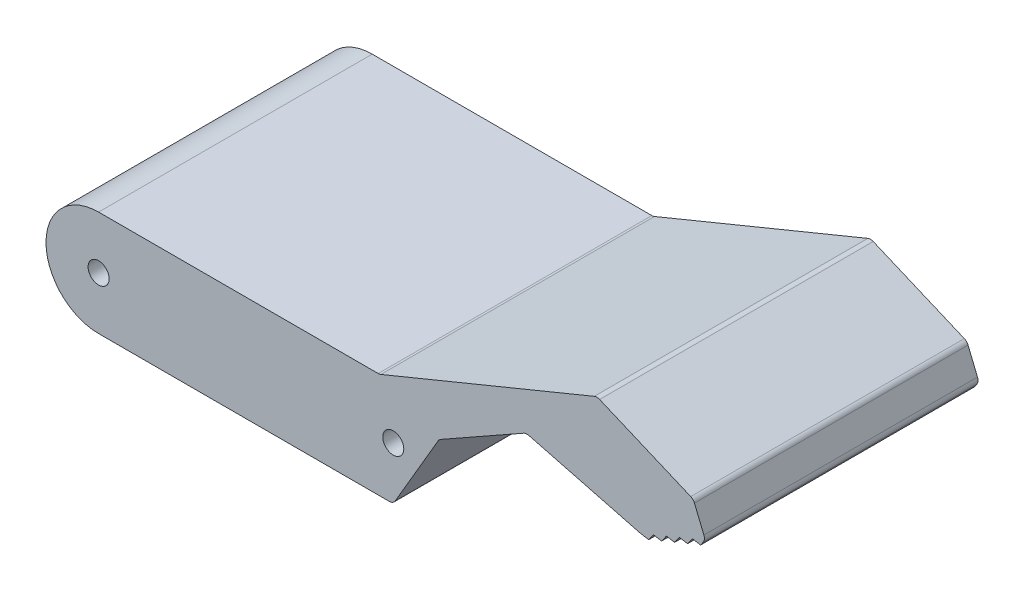
SolidWorks part; units mm, degrees
ref_plane "Front Plane" through (0, 0, 0) normal (0, 0, 1) x (1, 0, 0)
ref_plane "Top Plane" through (0, 0, 0) normal (0, 1, 0) x (1, 0, 0)
ref_plane "Right Plane" through (0, 0, 0) normal (1, 0, 0) x (0, 0, -1)
sketch "Sketch1" plane through (0, 0, 0) normal (0, 0, 1) x (1, 0, 0)
  line L0 (0, 0) -> (42, 0) construction
  line L1 (0, 7.5) -> (42, 7.5)
  line L2 (0, -7.5) -> (42, -7.5)
  line L3 (40.05, 7.5) -> (45.7937, -6.4698) construction
  line L4 (40.05, 7.5) -> (80.7446, 24.2316) construction
  line L5 (45.7937, -6.4698) -> (86.4883, 10.2618) construction
  line L6 (80.7446, 24.2316) -> (86.4883, 10.2618) construction
  line L7 (40.05, 7.5) -> (71.0334, 20.2388)
  line L8 (71.0334, 20.2388) -> (84.7771, 14.4238)
  line L9 (84.7771, 14.4238) -> (86.4883, 10.2618)
  line L10 (86.4883, 10.2618) -> (77.2395, 6.4592) construction
  line L11 (77.2395, 6.4592) -> (60.9298, 10.6906)
  line L12 (60.9298, 10.6906) -> (48.5305, 3.6881)
  line L13 (77.2395, 6.4592) -> (78.404, 6.2568)
  line L14 (78.404, 6.2568) -> (79.0893, 7.2197)
  line L15 (78.404, 6.2568) -> (85.803, 9.2989) construction
  line L16 (79.0893, 7.2197) -> (80.2537, 7.0173)
  line L17 (80.2537, 7.0173) -> (80.939, 7.9802)
  line L18 (80.939, 7.9802) -> (82.1035, 7.7778)
  line L19 (82.1035, 7.7778) -> (82.7888, 8.7408)
  line L20 (82.7888, 8.7408) -> (83.9532, 8.5383)
  line L21 (83.9532, 8.5383) -> (84.6386, 9.5013)
  line L22 (84.6386, 9.5013) -> (85.803, 9.2989)
  line L23 (85.803, 9.2989) -> (86.4883, 10.2618)
  line L24 (48.5305, 3.6881) -> (42, -7.5)
  arc A0 (0, 7.5) -> (0, -7.5) centre (0, 0) ccw
  arc A1 (42, -7.5) -> (42, 7.5) centre (42, 0) ccw
  circle A2 centre (0, 0) radius 1.5
  circle A3 centre (42, 0) radius 1.5
  point P3 (21, 0)
  dimension "D2" = 15
  dimension "D11" = 3
  dimension "D1" = 42
  dimension "D3" = 157.65
  dimension "D4" = 1.95
  dimension "D5" = 44
  dimension "D6" = 136
  dimension "D7" = 10
  dimension "D8" = 4.5
  dimension "D9" = 10.5
  dimension "D10" = 14.24
  dimension "D12" = 2
  dimension "D13" = 0.63
  dimension "D14" = 8
extrude "Boss-Extrude1" add sketch "Sketch1" along normal blind 39 contours L24 A1 L1 A0 L2 A3 A2 | A1 L12 L11 L13 L14 L16 L17 L18 L19 L20 L21 L22 L23 L9 L8 L7 L1
fillet "Fillet1" radius 1 8 edges at (48.5305, 3.6881, 19.5) (42, -7.5, 19.5) (60.9298, 10.6906, 19.5) (77.2395, 6.4592, 19.5) (86.4883, 10.2618, 19.5) (84.7771, 14.4238, 19.5) (71.0334, 20.2388, 19.5) (40.05, 7.5, 19.5)
